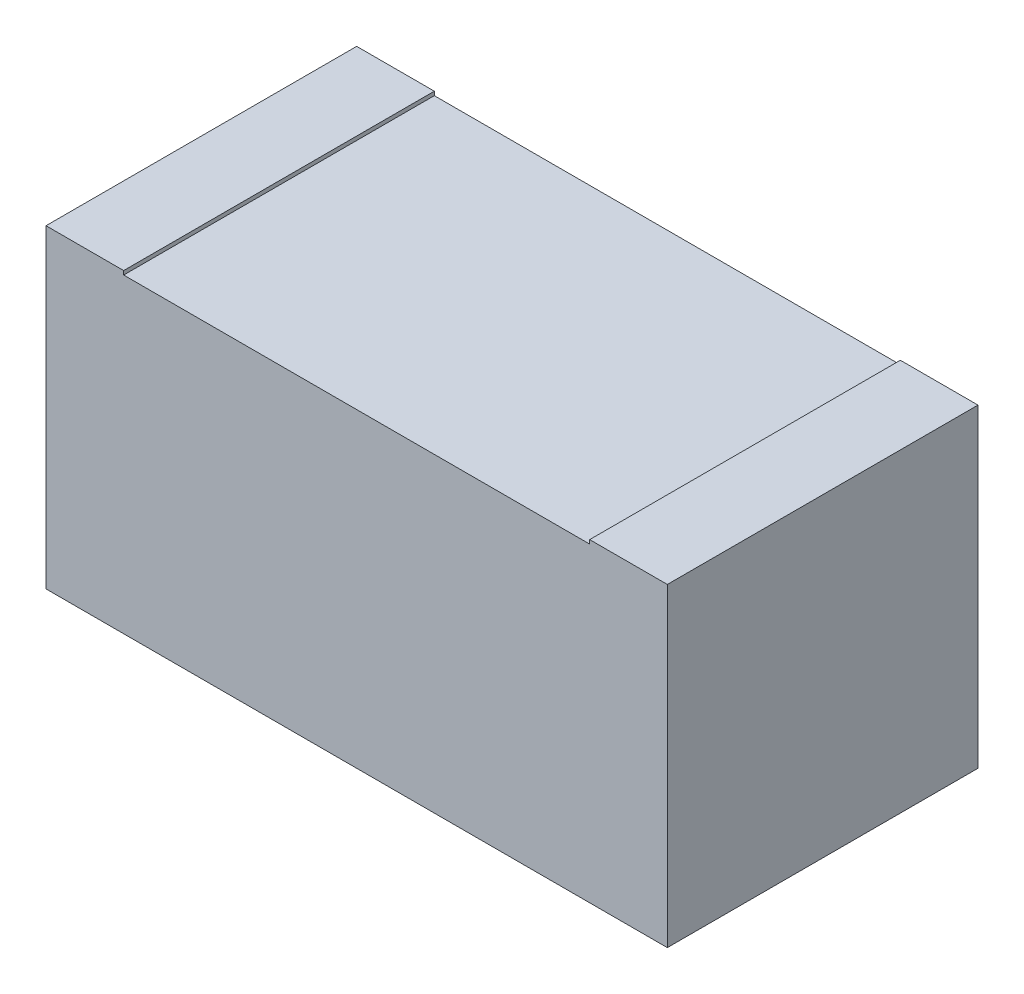
SolidWorks part; units mm, degrees
ref_plane "Спереди" through (0, 0, 0) normal (0, 0, 1) x (1, 0, 0)
ref_plane "Сверху" through (0, 0, 0) normal (0, 1, 0) x (1, 0, 0)
ref_plane "Справа" through (0, 0, 0) normal (1, 0, 0) x (0, 0, -1)
sketch "Эскиз1" plane through (0, 0, 0) normal (0, 1, 0) x (1, 0, 0)
  line L1 (-0.8538, 0.3697) -> (0.7462, 0.3697)
  line L2 (-0.8538, 0.3697) -> (-0.8538, -0.4303)
  line L3 (-0.8538, -0.4303) -> (0.7462, -0.4303)
  line L4 (0.7462, 0.3697) -> (0.7462, -0.4303)
  dimension "D1" = 1.6
  dimension "D2" = 0.8
extrude "Бобышка-Вытянуть1" add sketch "Эскиз1" along normal blind 0.8
sketch "Эскиз2" plane through (0, 0.8, 0) normal (0, 1, 0) x (1, 0, 0)
  line L0 (-0.8538, -0.4303) -> (0.7462, -0.4303) construction
  line L1 (-0.8538, 0.3697) -> (-0.6538, 0.3697)
  line L2 (-0.8538, 0.3697) -> (-0.8538, -0.4303)
  line L3 (-0.8538, -0.4303) -> (-0.6538, -0.4303)
  line L4 (-0.6538, 0.3697) -> (-0.6538, -0.4303)
  line L5 (0.7462, -0.4303) -> (0.7462, 0.3697) construction
  line L6 (0.7462, 0.3697) -> (0.5462, 0.3697)
  line L7 (0.7462, 0.3697) -> (0.7462, -0.4303)
  line L8 (0.7462, -0.4303) -> (0.5462, -0.4303)
  line L9 (0.5462, 0.3697) -> (0.5462, -0.4303)
  line L10 (0.7462, 0.3697) -> (-0.8538, 0.3697) construction
  dimension "D1" = 0.2
  dimension "D2" = 0.2
extrude "Бобышка-Вытянуть2" add sketch "Эскиз2" along normal blind 0.01
